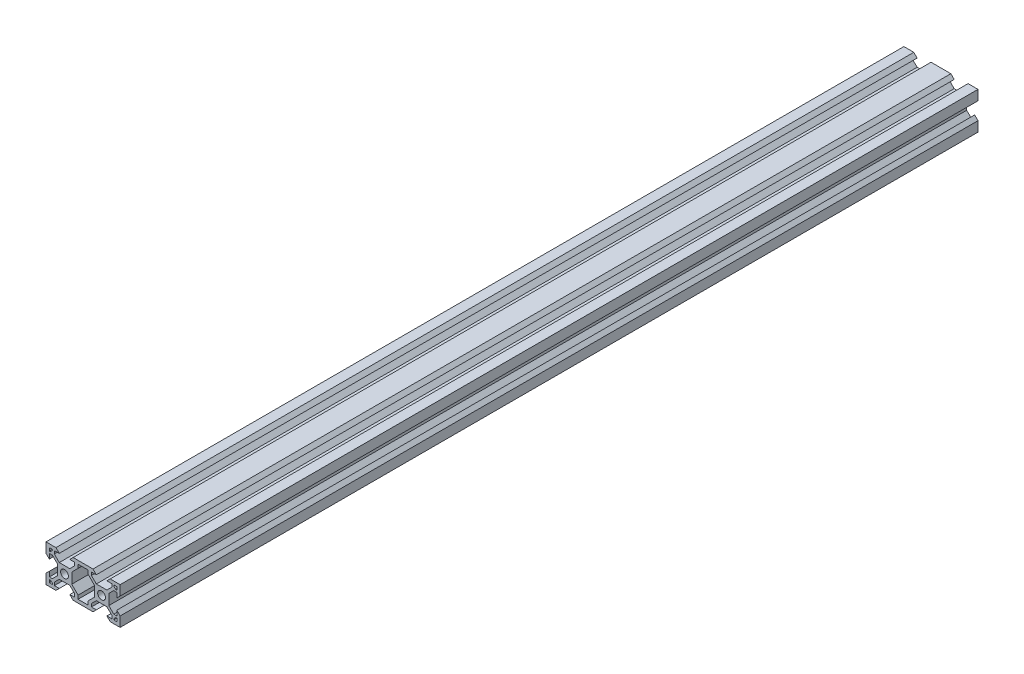
SolidWorks part; units mm, degrees
ref_plane "Front Plane" through (0, 0, 0) normal (0, 0, 1) x (1, 0, 0)
ref_plane "Top Plane" through (0, 0, 0) normal (0, 1, 0) x (1, 0, 0)
ref_plane "Right Plane" through (0, 0, 0) normal (1, 0, 0) x (0, 0, -1)
sketch "Sketch1" plane through (0, 0, 0) normal (0, 0, 1) x (1, 0, 0)
  line L0 (0, 0) -> (0, 5.36)
  line L1 (0, 20) -> (5.36, 20)
  line L3 (20, 0) -> (14.64, 0)
  line L4 (0, 10) -> (20, 10) construction
  line L5 (5.36, 0) -> (0, 0)
  line L6 (4.5007, 18.2) -> (7.16, 18.2)
  line L7 (17.3007, 3.76) -> (17.3007, 1.8)
  line L8 (15.4993, 1.8) -> (12.84, 1.8)
  line L9 (20, 0) -> (0, 0) construction
  line L10 (7.16, 1.8) -> (4.5007, 1.8)
  line L11 (15.4993, 3.44) -> (12.84, 6.0993)
  line L12 (4.5007, 16.56) -> (7.16, 13.9007)
  line L13 (13.9007, 12.84) -> (13.9007, 7.16)
  line L14 (12.84, 13.9007) -> (7.16, 13.9007)
  line L15 (6.0993, 12.84) -> (6.0993, 7.16)
  line L16 (7.16, 6.0993) -> (12.84, 6.0993)
  line L17 (4.5007, 16.56) -> (4.5007, 18.2)
  line L18 (3.44, 15.4993) -> (1.8, 15.4993)
  line L19 (4.5007, 3.44) -> (4.5007, 1.8)
  line L20 (3.44, 4.5007) -> (1.8, 4.5007)
  line L21 (15.4993, 3.44) -> (15.4993, 1.8)
  line L23 (17.3007, 1.8) -> (22.7007, 1.8)
  line L24 (15.4993, 16.56) -> (15.4993, 18.2)
  line L25 (7.16, 18.2) -> (5.36, 20)
  line L26 (12.84, 1.8) -> (14.64, 0)
  line L27 (7.16, 1.8) -> (5.36, 0)
  line L28 (12.84, 18.2) -> (14.64, 20)
  line L29 (1.8, 7.16) -> (0, 5.36)
  line L30 (1.8, 12.84) -> (0, 14.64)
  line L31 (22.7007, 1.8) -> (22.7007, 3.76)
  line L32 (17.3007, 16.24) -> (17.3007, 18.2)
  line L33 (17.3007, 18.2) -> (22.6993, 18.2)
  line L34 (22.6993, 18.2) -> (22.6993, 16.24)
  line L35 (38.2013, 12.8423) -> (40.001, 14.6427)
  line L36 (38.2024, 7.1623) -> (40.0028, 5.3627)
  line L37 (27.16, 18.2) -> (25.36, 20)
  line L38 (32.84, 1.8) -> (34.64, 0)
  line L39 (27.16, 1.8) -> (25.36, 0)
  line L40 (32.84, 18.2) -> (34.64, 20)
  line L41 (24.5013, 16.5597) -> (24.5009, 18.2)
  line L42 (1.8, 18.2) -> (3.4307, 18.2)
  line L43 (3.4307, 18.2) -> (3.4307, 17.63)
  line L44 (24.5038, 3.4397) -> (24.5041, 1.8)
  line L45 (36.5629, 4.5027) -> (38.2029, 4.503)
  line L46 (35.5025, 3.4418) -> (35.5028, 1.8)
  line L47 (36.5608, 15.5014) -> (38.2008, 15.5017)
  line L48 (35.4999, 16.5618) -> (35.4996, 18.2)
  line L49 (32.8426, 6.1006) -> (27.1626, 6.0995)
  line L50 (33.902, 12.8415) -> (33.9031, 7.1615)
  line L51 (27.1611, 13.9009) -> (32.8411, 13.902)
  line L52 (26.1007, 12.84) -> (26.1007, 7.16)
  line L53 (1.8, 4.5007) -> (1.8, 7.16)
  line L54 (24.5038, 3.4397) -> (27.1626, 6.0995)
  line L55 (35.5025, 3.4418) -> (32.8426, 6.1006)
  line L56 (36.5629, 4.5027) -> (33.9031, 7.1615)
  line L57 (24.5041, 1.8) -> (27.16, 1.8)
  line L58 (3.4307, 17.63) -> (2.37, 16.5693)
  line L59 (3.44, 4.5007) -> (6.0993, 7.16)
  line L60 (35.4996, 18.2) -> (32.84, 18.2)
  line L61 (20, 0) -> (25.36, 0)
  line L62 (39.9999, 20) -> (34.64, 20)
  line L63 (40.0038, 0) -> (40.0028, 5.3627)
  line L64 (1.8, 12.84) -> (1.8, 15.4993)
  line L65 (1.8, 1.8) -> (1.8, 18.2) construction
  line L66 (0, 14.64) -> (0, 20)
  line L67 (0, 0) -> (0, 20) construction
  line L68 (14.64, 20) -> (20, 20)
  line L69 (0, 20) -> (20, 20) construction
  line L70 (12.84, 18.2) -> (15.4993, 18.2)
  line L71 (1.8, 18.2) -> (18.2, 18.2) construction
  line L72 (25.36, 20) -> (20, 20)
  line L73 (27.16, 18.2) -> (24.5009, 18.2)
  line L74 (38.2013, 12.8423) -> (38.2008, 15.5017)
  line L75 (40.001, 14.6427) -> (39.9999, 20)
  line L76 (32.84, 1.8) -> (35.5028, 1.8)
  line L77 (34.64, 0) -> (40.0038, 0)
  line L78 (38.2029, 4.503) -> (38.2024, 7.1623)
  line L79 (35.4999, 16.5618) -> (32.8411, 13.902)
  line L80 (4.5007, 3.44) -> (7.16, 6.0993)
  line L81 (2.37, 16.5693) -> (1.8, 16.5693)
  line L82 (18.2, 1.8) -> (1.8, 1.8) construction
  line L83 (18.2, 18.2) -> (18.2, 1.8) construction
  line L84 (1.8, 16.5693) -> (1.8, 18.2)
  line L85 (20, 20) -> (20, 0) construction
  line L86 (1.8, 3.4307) -> (1.8, 1.8)
  line L87 (2.37, 3.4307) -> (1.8, 3.4307)
  line L88 (3.4307, 2.37) -> (2.37, 3.4307)
  line L89 (3.4307, 1.8) -> (3.4307, 2.37)
  line L90 (1.8, 1.8) -> (3.4307, 1.8)
  line L91 (13.9007, 7.16) -> (17.3007, 3.76)
  line L92 (20, 20) -> (20, -0.3542) construction
  line L93 (38.2, 1.8) -> (36.5693, 1.8)
  line L94 (36.5693, 1.8) -> (36.5693, 2.37)
  line L95 (36.5693, 2.37) -> (37.63, 3.4307)
  line L96 (37.63, 3.4307) -> (38.2, 3.4307)
  line L97 (38.2, 3.4307) -> (38.2, 1.8)
  line L98 (38.2, 16.5693) -> (38.2, 18.2)
  line L99 (37.63, 16.5693) -> (38.2, 16.5693)
  line L100 (36.5693, 17.63) -> (37.63, 16.5693)
  line L101 (36.5693, 18.2) -> (36.5693, 17.63)
  line L102 (38.2, 18.2) -> (36.5693, 18.2)
  line L103 (6.0993, 12.84) -> (3.44, 15.4993)
  line L104 (13.9007, 12.84) -> (17.3007, 16.24)
  line L105 (12.84, 13.9007) -> (15.4993, 16.56)
  line L106 (33.902, 12.8415) -> (36.5608, 15.5014)
  line L108 (27.1611, 13.9009) -> (24.5013, 16.5597)
  line L109 (26.1007, 12.84) -> (22.6993, 16.24)
  line L110 (26.1007, 7.16) -> (22.7007, 3.76)
  circle A0 centre (10, 10) radius 2.1
  circle A1 centre (30, 10) radius 2.1
  point P14 (17.3007, 3.76)
  point P81 (0, 0)
  point P82 (0, 0)
  point P112 (17.3007, 1.8)
  dimension "D3" = 4.2
  dimension "D1" = 20
  dimension "D2" = 20
  dimension "D5" = 5.4
  dimension "D7" = 1.07
  dimension "D8" = 45
  dimension "D9" = 1.5
  dimension "D10" = 4.5007
  dimension "D11" = 5.68
  dimension "D12" = 5.68
  dimension "D13" = 5.68
  dimension "D14" = 5.68
  dimension "D15" = 1.64
  dimension "D16" = 1.64
  dimension "D17" = 1.64
  dimension "D18" = 1.64
  dimension "D19" = 1.64
  dimension "D20" = 15.4993
  dimension "D21" = 1.07
  dimension "D22" = 1.64
  dimension "D23" = 45
  dimension "D24" = 45
  dimension "D25" = 1.5
  dimension "D26" = 45
  dimension "D27" = 45
  dimension "D28" = 45
  dimension "D4" = 1.8
extrude "Boss-Extrude1" add sketch "Sketch1" against normal blind 463
